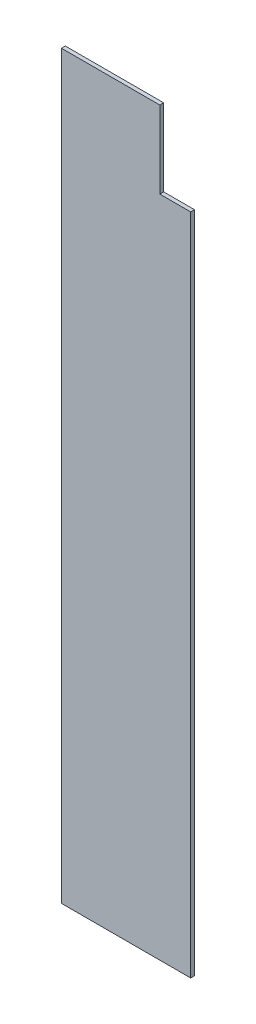
SolidWorks part; units mm, degrees
material "PE High Density"
ref_plane "Front Plane" through (0, 0, 0) normal (0, 0, 1) x (1, 0, 0)
ref_plane "Top Plane" through (0, 0, 0) normal (0, 1, 0) x (1, 0, 0)
ref_plane "Right Plane" through (0, 0, 0) normal (1, 0, 0) x (0, 0, -1)
sketch "Sketch1" plane through (0, 0, 0) normal (0, 0, 1) x (1, 0, 0)
  line L0 (381, 1219.2) -> (381, 0) construction
  line L3 (168.275, 1219.2) -> (330.2, 1219.2)
  line L4 (381, 0) -> (381, 1092.2)
  line L7 (381, 1092.2) -> (330.2, 1092.2)
  line L8 (330.2, 1219.2) -> (330.2, 1092.2)
  line L9 (381, 0) -> (168.275, 0)
  line L11 (168.275, 1219.2) -> (168.275, 0)
  dimension "D1" = 127
  dimension "D2" = 50.8
  dimension "D3" = 50.8
  dimension "D4" = 1092.2
  dimension "D5" = 212.725
extrude "Boss-Extrude1" add sketch "Sketch1" along normal blind 6.35
